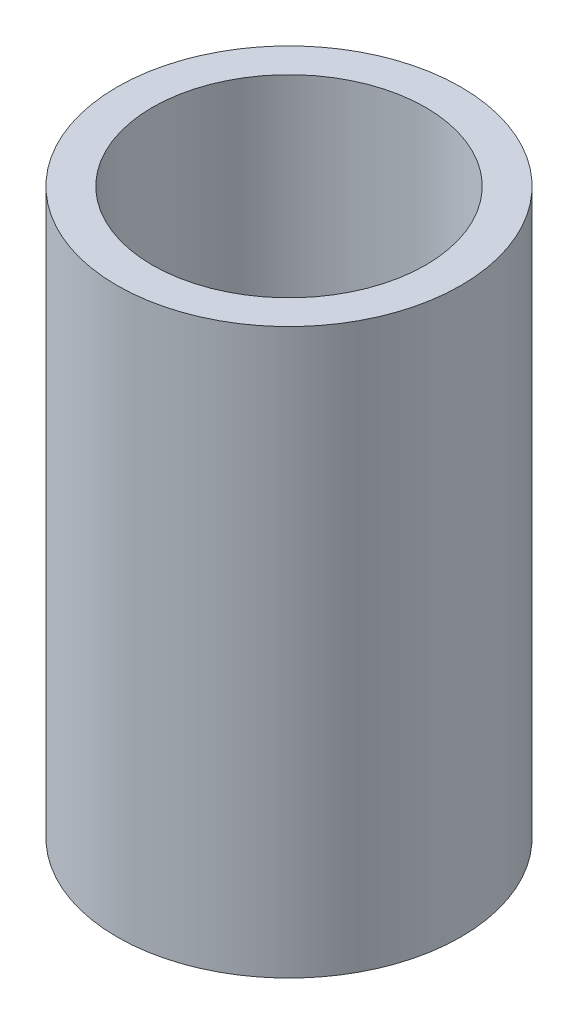
SolidWorks part; units mm, degrees
ref_plane "Front Plane" through (0, 0, 0) normal (0, 0, 1) x (1, 0, 0)
ref_plane "Top Plane" through (0, 0, 0) normal (0, 1, 0) x (1, 0, 0)
ref_plane "Right Plane" through (0, 0, 0) normal (1, 0, 0) x (0, 0, -1)
sketch "Sketch1" plane through (0, 0, 0) normal (0, 1, 0) x (1, 0, 0)
  circle A0 centre (0, 0) radius 12.3031
  circle A1 centre (0, 0) radius 15.4781
  dimension "D1" = 24.6062
  dimension "D2" = 3.175
extrude "Boss-Extrude1" add sketch "Sketch1" along normal blind 50.8 contours A1 A0
